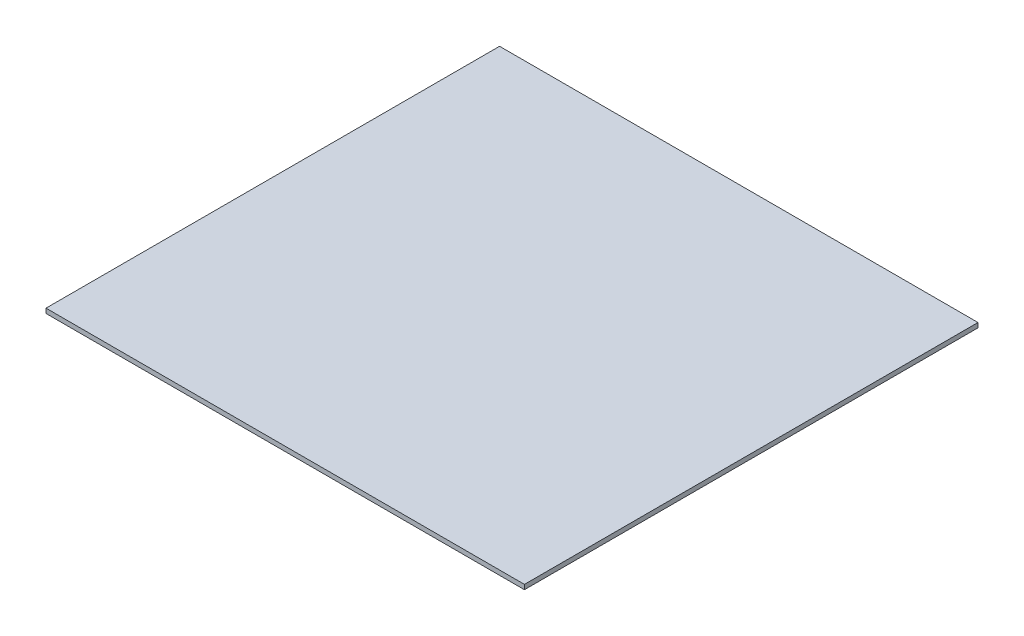
SolidWorks part; units mm, degrees
ref_plane "Front Plane" through (0, 0, 0) normal (0, 0, 1) x (1, 0, 0)
ref_plane "Top Plane" through (0, 0, 0) normal (0, 1, 0) x (1, 0, 0)
ref_plane "Right Plane" through (0, 0, 0) normal (1, 0, 0) x (0, 0, -1)
sketch "Sketch1" plane through (0, 0, 0) normal (0, 1, 0) x (1, 0, 0)
  line L1 (-163.5, -155) -> (163.5, -155)
  line L2 (-163.5, -155) -> (-163.5, 155)
  line L3 (-163.5, 155) -> (163.5, 155)
  line L4 (163.5, -155) -> (163.5, 155)
  line L5 (-163.5, -155) -> (163.5, 155) construction
  line L6 (-163.5, 155) -> (163.5, -155) construction
  point P0 (0, 0)
  dimension "D1" = 327
  dimension "D2" = 310
extrude "Boss-Extrude1" add sketch "Sketch1" along normal blind 3.175
